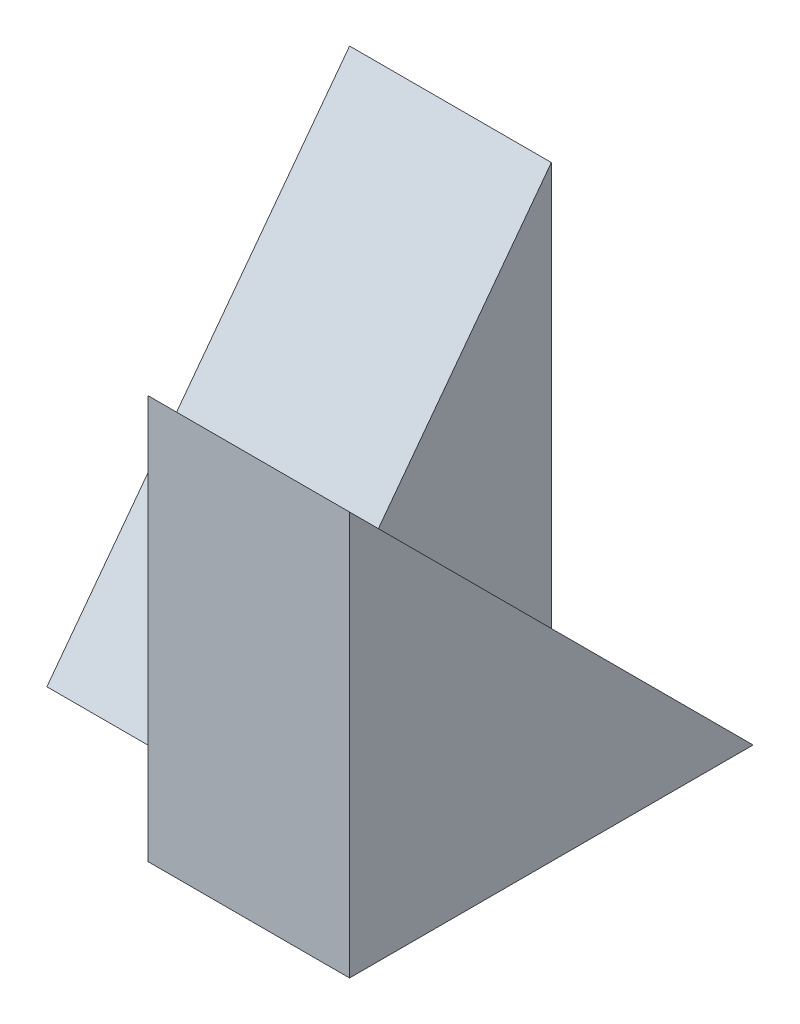
SolidWorks part; units mm, degrees
ref_plane "Front Plane" through (0, 0, 0) normal (0, 0, 1) x (1, 0, 0)
ref_plane "Top Plane" through (0, 0, 0) normal (0, 1, 0) x (1, 0, 0)
ref_plane "Right Plane" through (0, 0, 0) normal (1, 0, 0) x (0, 0, -1)
sketch "Sketch1" plane through (0, 0, 0) normal (1, 0, 0) x (0, 0, -1)
  line L1 (0, 0) -> (4, 0)
  line L2 (0, 0) -> (0, 4)
  line L3 (0, 4) -> (4, 4)
  line L4 (4, 0) -> (4, 4)
  dimension "D1" = 4
  dimension "D2" = 4
extrude "Boss-Extrude1" add sketch "Sketch1" along normal blind 2
sketch "Sketch2" plane through (0, 0, 0) normal (-1, 0, 0) x (0, 0, 1)
  line L0 (-1, 0) -> (-1, 4)
  line L1 (0, 0) -> (-4, 0) construction
  line L2 (-4, 0) -> (-4, 4) construction
  line L3 (-4, 4) -> (-4, 0)
  line L4 (-4, 0) -> (-1, 0)
  line L5 (-4, 4) -> (0, 4) construction
  line L6 (-1, 4) -> (-4, 4)
  dimension "D1" = 3
  dimension "D2" = 4
extrude "Boss-Extrude2" add sketch "Sketch2" along normal blind 2
sketch "Sketch3" plane through (2, 0, 0) normal (1, 0, 0) x (0, 0, -1)
  line L0 (4, 0) -> (0, 4)
  line L1 (0, 4) -> (0, 0) construction
  line L2 (0, 4) -> (4, 4)
  line L3 (4, 4) -> (4, 0)
extrude "Cut-Extrude1" cut sketch "Sketch3" against normal blind 2
sketch "Sketch4" plane through (-2, 0, 0) normal (-1, 0, 0) x (0, 0, 1)
  line L0 (-1, 0) -> (-4, 4)
  line L1 (-4, 4) -> (-1, 4)
  line L2 (-1, 4) -> (-1, 0)
extrude "Cut-Extrude2" cut sketch "Sketch4" against normal blind 2
